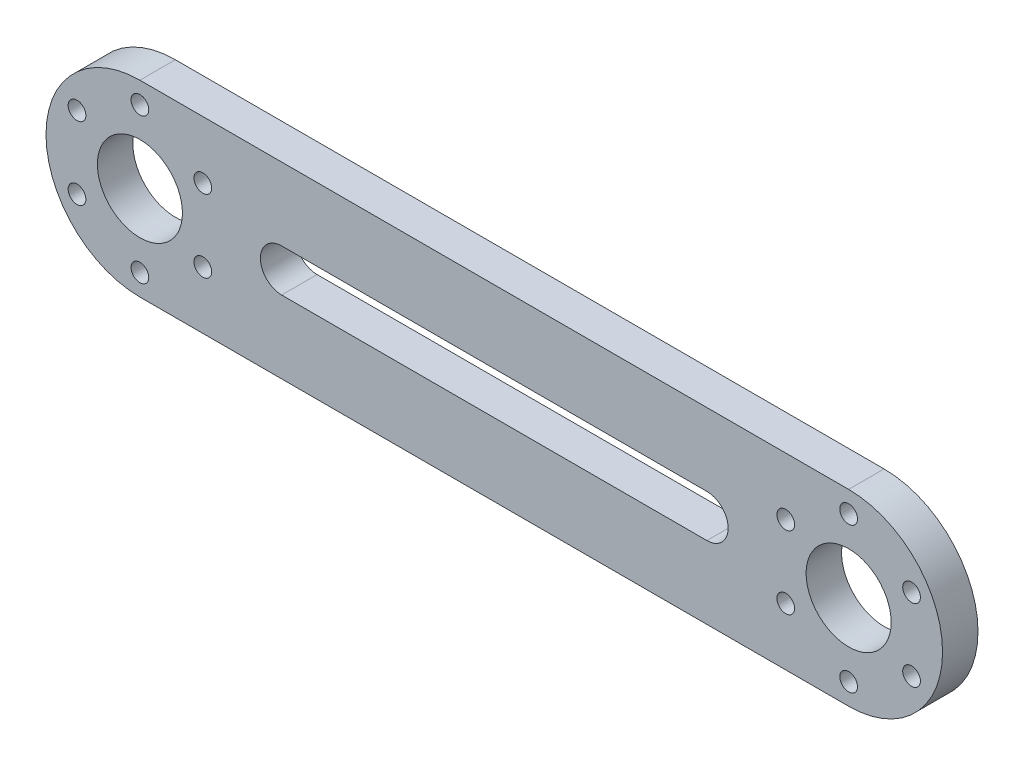
SolidWorks part; units mm, degrees
material "Wrought Stainless Steel"
ref_plane "Front Plane" through (0, 0, 0) normal (0, 0, 1) x (1, 0, 0)
ref_plane "Top Plane" through (0, 0, 0) normal (0, 1, 0) x (1, 0, 0)
ref_plane "Right Plane" through (0, 0, 0) normal (1, 0, 0) x (0, 0, -1)
sketch "Sketch1" plane through (0, 0, 0) normal (0, 0, 1) x (1, 0, 0)
  line L0 (0, 13.25) -> (100, 13.25)
  line L1 (0, -13.25) -> (100, -13.25)
  line L2 (50, 0) -> (50, -3)
  line L3 (50, 0) -> (50, 3)
  line L4 (20, 3) -> (80, 3)
  line L5 (20, -3) -> (80, -3)
  circle A0 centre (0, 0) radius 13.25
  circle A1 centre (100, 0) radius 13.25
  circle A2 centre (0, 0) radius 6
  circle A3 centre (100, 0) radius 6
  circle A4 centre (20, 0) radius 3
  circle A5 centre (80, 0) radius 3
  point P18 (50, 3)
  point P21 (50, -3)
extrude "Boss-Extrude1" add sketch "Sketch1" along normal blind 5 contours A0 A2 | A1 L0 A0 L1 A5 L5 A4 L4 | A1 A3
sketch "Sketch2" plane through (0, 0, 5) normal (0, 0, 1) x (1, 0, 0)
  line L0 (0, 0) -> (8.8768, 5.125)
  line L1 (0, 0) -> (8.8768, -5.125)
  line L2 (0, 0) -> (-8.8768, 5.125)
  line L3 (0, 0) -> (-8.8768, -5.125)
  line L4 (0, 10.25) -> (0, -10.25)
  line L5 (50, 13.25) -> (50, -13.25) construction
  line L6 (0, 13.25) -> (100, 13.25) construction
  line L7 (0, -13.25) -> (100, -13.25) construction
  circle A0 centre (0, 0) radius 10.25
  circle A1 centre (0, 10.25) radius 1.25
  circle A2 centre (0, -10.25) radius 1.25
  circle A3 centre (8.8768, 5.125) radius 1.25
  circle A4 centre (8.8768, -5.125) radius 1.25
  circle A5 centre (-8.8768, 5.125) radius 1.25
  circle A6 centre (-8.8768, -5.125) radius 1.25
  circle A7 centre (100, -10.25) radius 1.25
  circle A8 centre (108.8768, -5.125) radius 1.25
  circle A9 centre (108.8768, 5.125) radius 1.25
  circle A10 centre (100, 10.25) radius 1.25
  circle A11 centre (91.1232, 5.125) radius 1.25
  circle A12 centre (91.1232, -5.125) radius 1.25
extrude "Cut-Extrude1" cut sketch "Sketch2" against normal through all contours A10 | A9 | A3 | A4 | A5 | A6 | A2 | A1 | A11 | A8 | A7 | A12
